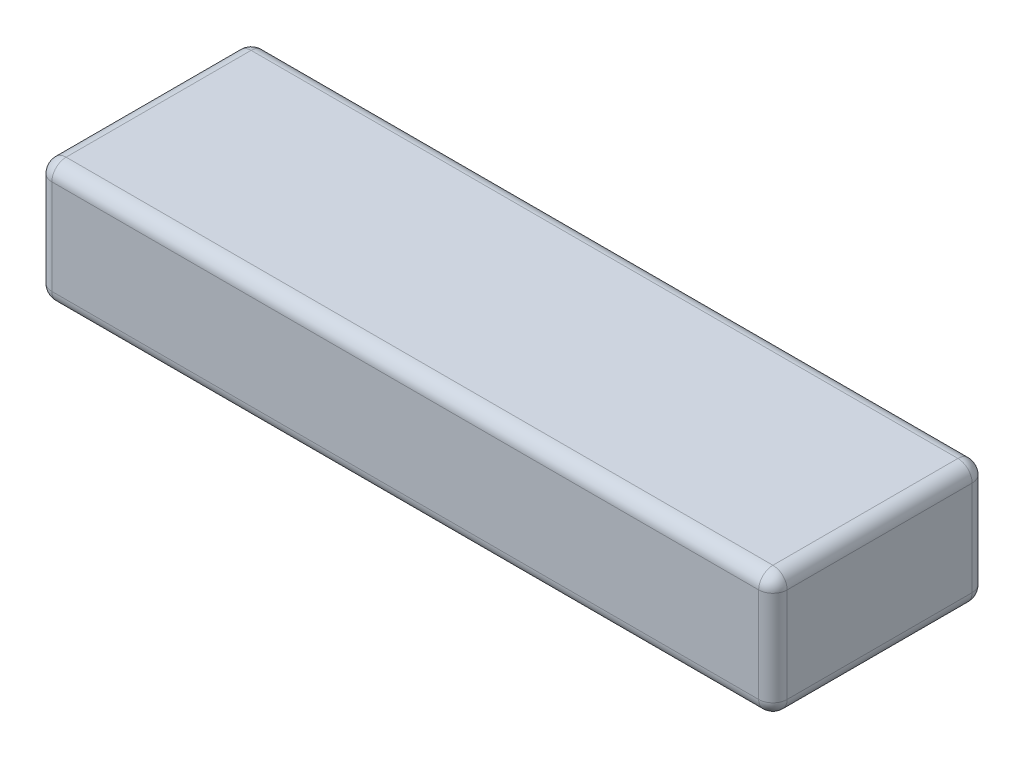
SolidWorks part; units mm, degrees
material "Plastique personnalisé"
ref_plane "Plan de face" through (0, 0, 0) normal (0, 0, 1) x (1, 0, 0)
ref_plane "Plan de dessus" through (0, 0, 0) normal (0, 1, 0) x (1, 0, 0)
ref_plane "Plan de droite" through (0, 0, 0) normal (1, 0, 0) x (0, 0, -1)
sketch "Esquisse1" plane through (0, 0, 0) normal (0, 1, 0) x (1, 0, 0)
  line L1 (-155, 22.5) -> (0, 22.5)
  line L2 (-155, 22.5) -> (-155, -22.5)
  line L3 (-155, -22.5) -> (0, -22.5)
  line L4 (0, 22.5) -> (0, -22.5)
  dimension "D1" = 155
  dimension "D2" = 45
extrude "Boss.-Extru.1" add sketch "Esquisse1" along normal blind 26
fillet "Congé1" radius 3 12 edges at (-155, 13, -22.5) (-77.5, 26, -22.5) (-155, 26, 0) (-155, 13, 22.5) (-77.5, 0, 22.5) (-155, 0, 0) (-77.5, 0, -22.5) (0, 13, -22.5) (0, 0, 0) (0, 13, 22.5) (0, 26, 0) (-77.5, 26, 22.5)
